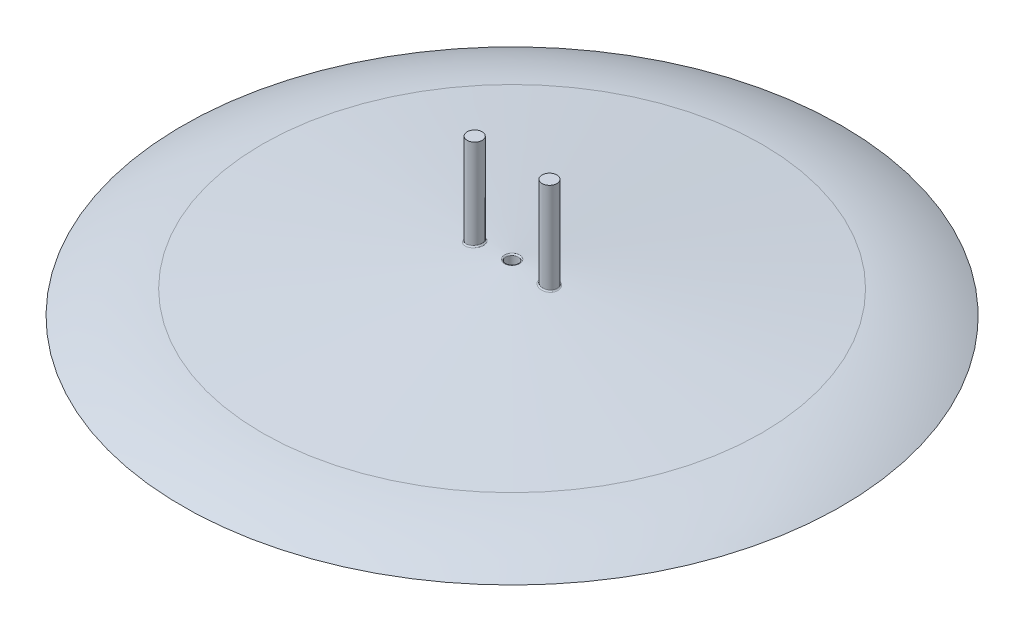
SolidWorks part; units mm, degrees
ref_plane "Front Plane" through (0, 0, 0) normal (0, 0, 1) x (1, 0, 0)
ref_plane "Top Plane" through (0, 0, 0) normal (0, 1, 0) x (1, 0, 0)
ref_plane "Right Plane" through (0, 0, 0) normal (1, 0, 0) x (0, 0, -1)
sketch "Sketch1" plane through (0, 0, 0) normal (0, 0, 1) x (1, 0, 0)
  line L1 (0, 0) -> (0, 40)
  line L2 (0, 0) -> (264.425, 0)
  line L4 (0, 40) -> (200.5374, 19.0164)
  arc A0 (264.425, 0) -> (200.5374, 19.0164) centre (181.686, -161.1435) ccw
  point P9 (264.425, 0)
revolve "Revolve2" add sketch "Sketch1" angle 360 about L1
shell "Shell1" thickness 10
sketch "Sketch2" plane through (0, 0, 0) normal (0, 1, 0) x (1, 0, 0)
  circle A0 centre (0, 0) radius 5
extrude "Cut-Extrude1" cut sketch "Sketch2" along normal through all
ref_plane "Plane1" through (0, 110, 0) normal (0, 1, 0) x (1, 0, 0)
sketch "Sketch3" plane through (0, 110, 0) normal (0, 1, 0) x (1, 0, 0)
  circle A1 centre (30, 0) radius 6
  circle A2 centre (-30, 0) radius 6
extrude "Boss-Extrude1" add sketch "Sketch3" against normal up to surface (73.2013 mm away)
cosmetic thread "Cosmetic Thread1" parameters "D1"=20, "D2"=10.106
cosmetic thread "Cosmetic Thread2" parameters "D1"=20, "D2"=10.106
fillet "Fillet1" radius 1 1 edges at (-24.9472, 37.3677, 3.2356)
fillet "Fillet2" radius 1 1 edges at (35.1203, 36.3106, 3.1278)
fillet "Fillet3" radius 1 1 edges at (0, 39.4768, -5)
fillet "Fillet4" radius 1 1 edges at (0, 29.4222, -5)
